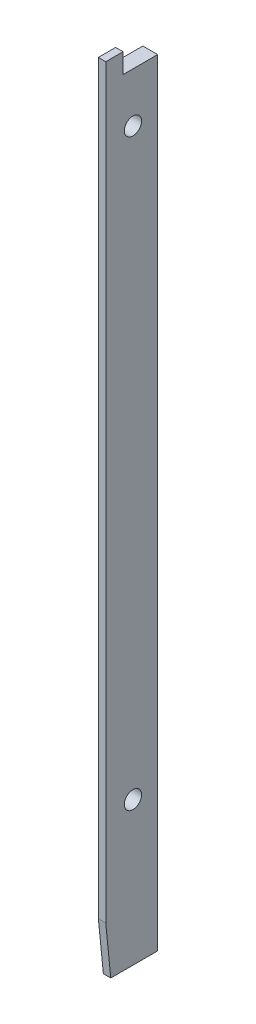
SolidWorks part; units mm, degrees
ref_plane "Front Plane" through (0, 0, 0) normal (0, 0, 1) x (1, 0, 0)
ref_plane "Top Plane" through (0, 0, 0) normal (0, 1, 0) x (1, 0, 0)
ref_plane "Right Plane" through (0, 0, 0) normal (1, 0, 0) x (0, 0, -1)
sketch "Sketch1" plane through (0, 0, 0) normal (0, 1, 0) x (1, 0, 0)
  line L1 (0, 0) -> (3, 0)
  line L2 (0, 0) -> (0, 7)
  line L3 (0, 7) -> (3, 7)
  line L4 (3, 0) -> (3, 7)
  dimension "D1" = 7
  dimension "D2" = 3
extrude "Boss-Extrude1" add sketch "Sketch1" along normal blind 157
sketch "Sketch2" plane through (0, 0, 0) normal (0, 0, 1) x (1, 0, 0)
  line L1 (1.5, 161) -> (3, 161)
  line L2 (1.5, 161) -> (1.5, 0)
  line L3 (1.5, 0) -> (3, 0)
  line L4 (3, 161) -> (3, 0)
  point P5 (1.421, 159.0944)
  dimension "D1" = 1.5
  dimension "D2" = 161
extrude "Boss-Extrude2" add sketch "Sketch2" along normal blind 3.5
sketch "Sketch3" plane through (3, 0, 0) normal (1, 0, 0) x (0, 0, -1)
  line L0 (7, 157) -> (7, 0) construction
  line L1 (0, 157) -> (7, 157) construction
  circle A0 centre (2, 147) radius 1.75
  circle A1 centre (2, 29) radius 1.75
  point P4 (0, 0)
  point P5 (0, 0)
  dimension "D1" = 3.5
  dimension "D2" = 5
  dimension "D4" = 118
  dimension "D3" = 10
extrude "Cut-Extrude1" cut sketch "Sketch3" against normal through all
sketch "Sketch4" plane through (3, 0, 0) normal (1, 0, 0) x (0, 0, -1)
  line L0 (-2.4852, 0) -> (-3.5, 10.1494)
  line L5 (-3.5, 0) -> (7, 0) construction
  line L6 (-3.5, 0) -> (-3.5, 161) construction
  line L13 (-3.5, 0) -> (7, 0)
  line L14 (7, 0) -> (7, 157)
  line L15 (7, 157) -> (0, 157)
  line L16 (0, 157) -> (0, 161)
  line L17 (0, 161) -> (-3.5, 161)
  line L18 (-3.5, 161) -> (-3.5, 0)
  line L19 (-3.5, 0) -> (-2.4852, 0)
  line L24 (-3.5, 10.1494) -> (-3.5, 0)
  point P2 (0, 0)
  point P3 (-2.6764, 14.5988)
  point P4 (0, 0)
  point P5 (1.5237, 15.2389)
  point P7 (-3.5, 14.7919)
  point P10 (3.2257, 0)
  point P11 (-1.6922, 0)
  point P12 (-1.5294, 0)
  point P13 (0, 0)
  point P16 (0, 0)
  dimension "D1" = 95.71
  dimension "D2" = 10.2
  dimension "D3" = 0
extrude "Cut-Extrude2" cut sketch "Sketch4" against normal through all
